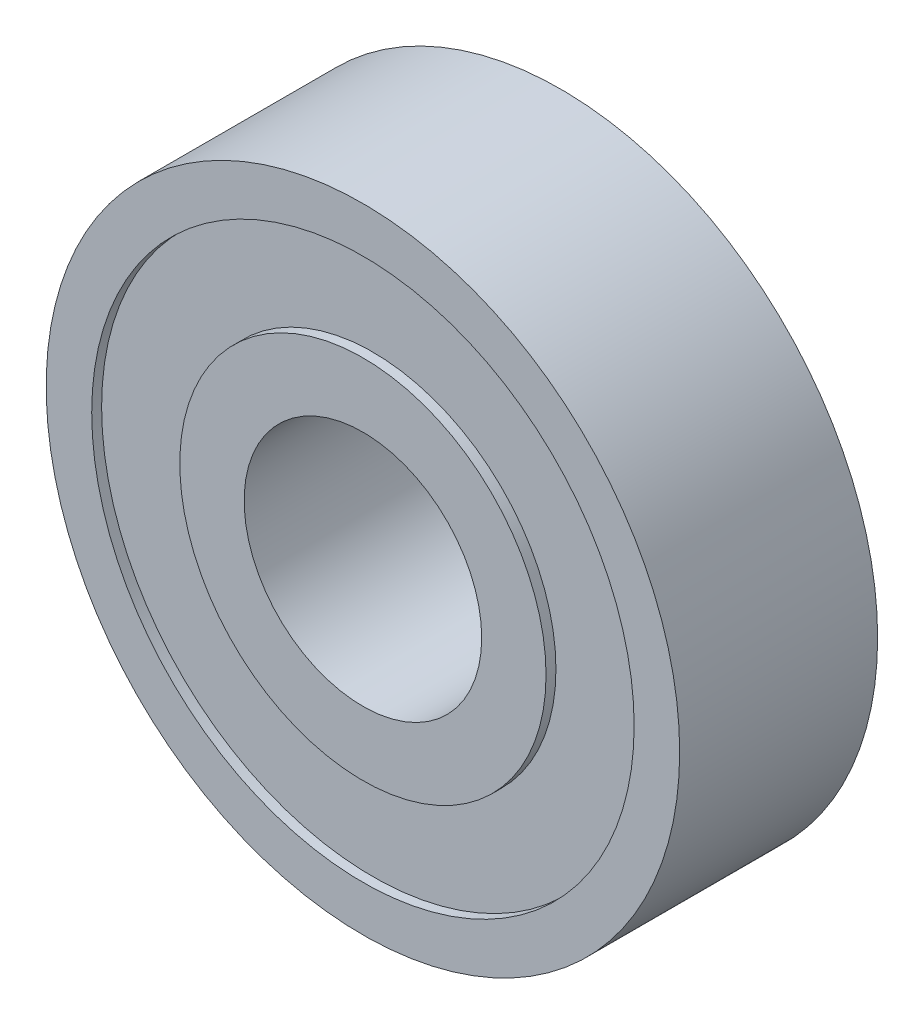
SolidWorks part; units mm, degrees
material "201 退火不鏽鋼 (SS)"
ref_plane "前基準面" through (0, 0, 0) normal (0, 0, 1) x (1, 0, 0)
ref_plane "上基準面" through (0, 0, 0) normal (0, 1, 0) x (1, 0, 0)
ref_plane "右基準面" through (0, 0, 0) normal (1, 0, 0) x (0, 0, -1)
sketch "草圖1" plane through (0, 0, 0) normal (0, 0, 1) x (1, 0, 0)
  circle A0 centre (0, 0) radius 16
  dimension "D1" = 32
extrude "填料-伸長1" add sketch "草圖1" along normal mid plane 10
sketch "草圖2" plane through (0, 0, 5) normal (0, 0, 1) x (1, 0, 0)
  circle A0 centre (0, 0) radius 6
  dimension "D1" = 12
extrude "除料-伸長1" cut sketch "草圖2" against normal through all
sketch "草圖3" plane through (0, 0, 5) normal (0, 0, 1) x (1, 0, 0)
  circle A0 centre (0, 0) radius 9.25
  circle A1 centre (0, 0) radius 13.7
  dimension "D1" = 27.4
  dimension "D2" = 18.5
extrude "除料-伸長2" cut sketch "草圖3" against normal blind 0.5
mirror "鏡射1" about plane through (0, 0, 0) normal (0, 0, 1) of "除料-伸長2"
